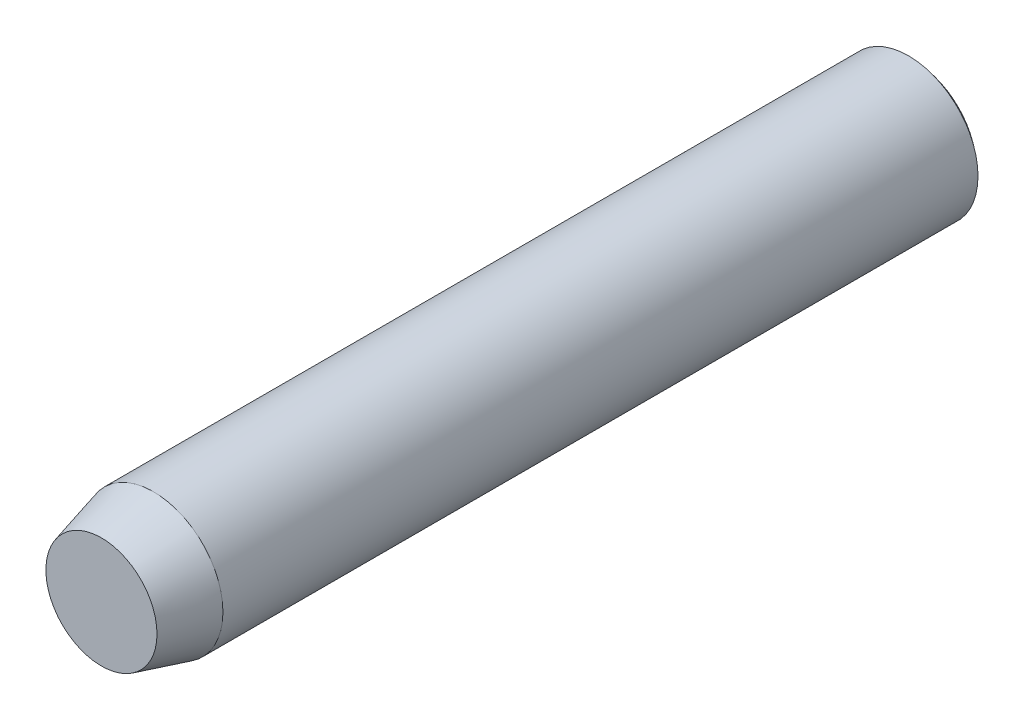
SolidWorks part; units mm, degrees
material "acero"
ref_plane "Alzado" through (0, 0, 0) normal (0, 0, 1) x (1, 0, 0)
ref_plane "Planta" through (0, 0, 0) normal (0, 1, 0) x (1, 0, 0)
ref_plane "Vista lateral" through (0, 0, 0) normal (1, 0, 0) x (0, 0, -1)
sketch "Croquis1" plane through (0, 0, 0) normal (0, 0, 1) x (1, 0, 0)
  circle A0 centre (0, 0) radius 2
  dimension "D1" = 4
extrude "Saliente-Extruir1" add sketch "Croquis1" along normal blind 24
sketch "Croquis2" plane through (0, 0, 0) normal (0, 1, 0) x (1, 0, 0)
  line L0 (-2, 0) -> (-2, -24) construction
  line L2 (-2, -0.75) -> (-2, 0)
  line L3 (-2, 0) -> (0, 0) construction
  line L4 (-2, 0) -> (-2, 0.2)
  line L5 (-2, 0.2) -> (0, 0.2)
  line L6 (0, 0.2) -> (0, 0)
  arc A0 (-2, -0.75) -> (0, 0) centre (0, -3.0417) cw
  dimension "D1" = 0.75
  dimension "D2" = 0.2
ref_axis "Eje1" through (0, 0, 24) along (0, 0, -1)
revolve "Cortar-Revolución3" cut sketch "Croquis2" angle 360 about axis through (0, 0, 24) along (0, 0, -1)
chamfer "Chaflán1" distance 1.5 distance2 0.4 1 edges at (2, 0, 24)
